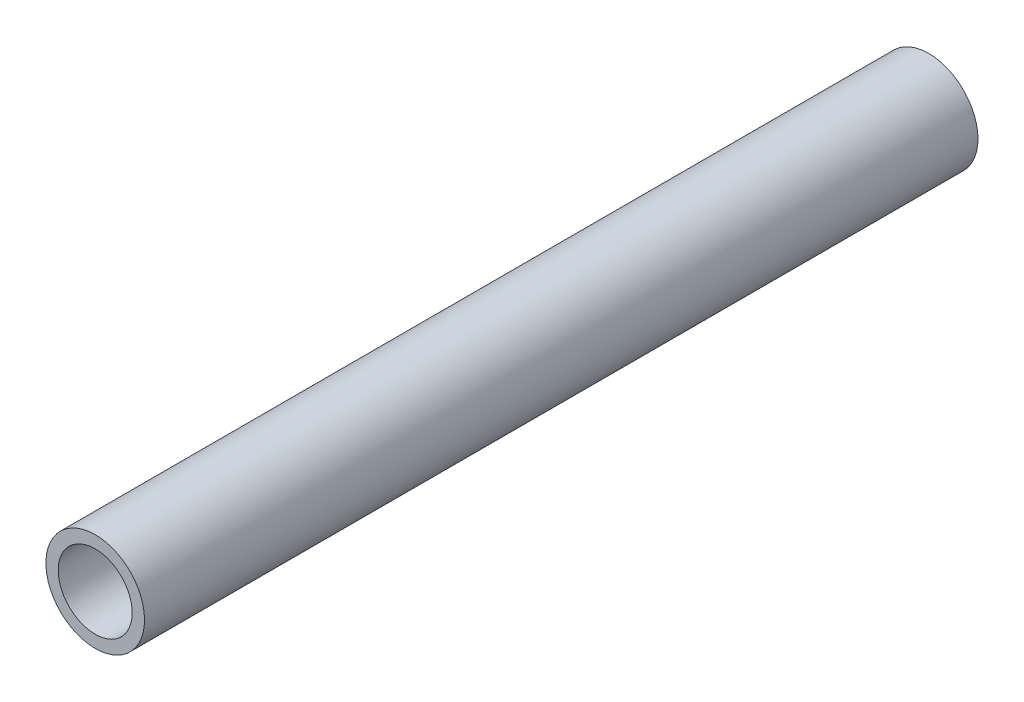
SolidWorks part; units mm, degrees
material "SS 304 (Default)"
ref_plane "Front Plane" through (0, 0, 0) normal (0, 0, 1) x (1, 0, 0)
ref_plane "Top Plane" through (0, 0, 0) normal (0, 1, 0) x (1, 0, 0)
ref_plane "Right Plane" through (0, 0, 0) normal (1, 0, 0) x (0, 0, -1)
sketch "Sketch1" plane through (0, 0, 0) normal (0, 0, 1) x (1, 0, 0)
  circle A0 centre (0, 0) radius 12.7
  circle A1 centre (0, 0) radius 9.525
  dimension "D1" = 3.175
  dimension "Diameter" = 25.4
extrude "Extrude1" add sketch "Sketch1" along normal mid plane 214.6935
